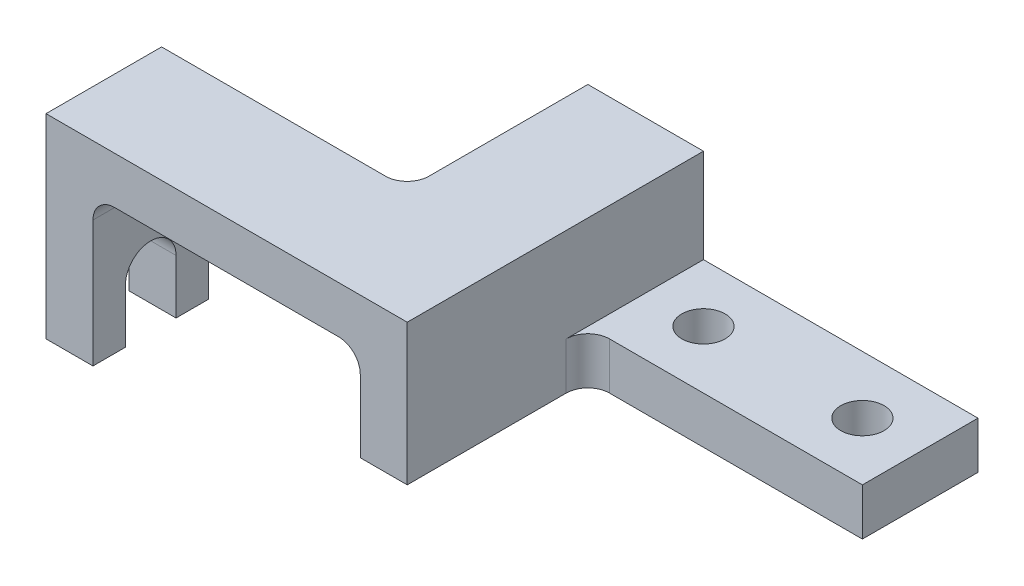
SolidWorks part; units mm, degrees
material "회주철"
ref_plane "정면" through (0, 0, 0) normal (0, 0, 1) x (1, 0, 0)
ref_plane "윗면" through (0, 0, 0) normal (0, 1, 0) x (1, 0, 0)
ref_plane "우측면" through (0, 0, 0) normal (1, 0, 0) x (0, 0, -1)
sketch "스케치1" plane through (0, 0, 0) normal (0, 1, 0) x (1, 0, 0)
  line L0 (0, 32) -> (68, 32)
  line L1 (0, 0) -> (100, 0)
  line L2 (0, 0) -> (0, 32)
  line L3 (68, 82) -> (176, 82)
  line L5 (100, 50) -> (176, 50)
  line L6 (100, 0) -> (100, 50)
  line L7 (176, 50) -> (176, 82)
  line L8 (68, 32) -> (68, 82)
  line L9 (0, 32) -> (176, 32) construction
  line L10 (0, 0) -> (176, 0) construction
  line L11 (0, 50) -> (176, 50) construction
  line L12 (68, 0) -> (68, 82) construction
  line L13 (100, 0) -> (100, 82) construction
  line L14 (0, 82) -> (176, 82) construction
  circle A0 centre (116, 66) radius 6
  circle A1 centre (160, 66) radius 6
  dimension "D1" = 12
  dimension "D2" = 100
  dimension "D3" = 116
  dimension "D4" = 160
  dimension "D5" = 32
  dimension "D6" = 66
  dimension "D7" = 108
  dimension "D8" = 82
  dimension "D9" = 76
extrude "보스-돌출1" add sketch "스케치1" along normal blind 54
fillet "필렛1" radius 6 2 edges at (100, 27, -50) (68, 27, -32)
sketch "스케치2" plane through (0, 0, 0) normal (0, 0, 1) x (1, 0, 0)
  line L0 (87, 35) -> (87, 15)
  line L1 (100, 15) -> (176, 15) construction
  line L2 (100, 41) -> (100, 15) construction
  line L3 (13, 35) -> (13, 0)
  line L4 (87, 41) -> (87, 15) construction
  line L6 (19, 41) -> (81, 41)
  line L7 (100, 28) -> (176, 28)
  line L8 (87, 15) -> (176, 15)
  line L10 (100, 54) -> (100, 28)
  line L11 (176, 15) -> (176, 0)
  line L12 (176, 0) -> (13, 0)
  line L13 (176, 28) -> (176, 54)
  line L15 (176, 54) -> (100, 54)
  arc A0 (87, 35) -> (81, 41) centre (81, 35) ccw
  arc A1 (13, 35) -> (19, 41) centre (19, 35) cw
  dimension "D1" = 6
  dimension "D2" = 13
  dimension "D3" = 87
  dimension "D4" = 15
  dimension "D5" = 28
  dimension "D6" = 41
extrude "컷-돌출1" cut sketch "스케치2" against normal through all
sketch "스케치3" plane through (0, 0, 0) normal (1, 0, 0) x (0, 0, -1)
  line L4 (23, 15) -> (23, 0)
  line L6 (32, 0) -> (0, 0) construction
  line L7 (9, 15) -> (9, 0)
  line L11 (23, 0) -> (9, 0)
  arc A0 (23, 15) -> (9, 15) centre (16, 15) ccw
  dimension "D1" = 7
  dimension "D2" = 16
  dimension "D3" = 15
extrude "컷-돌출2" cut sketch "스케치3" along normal up to next
